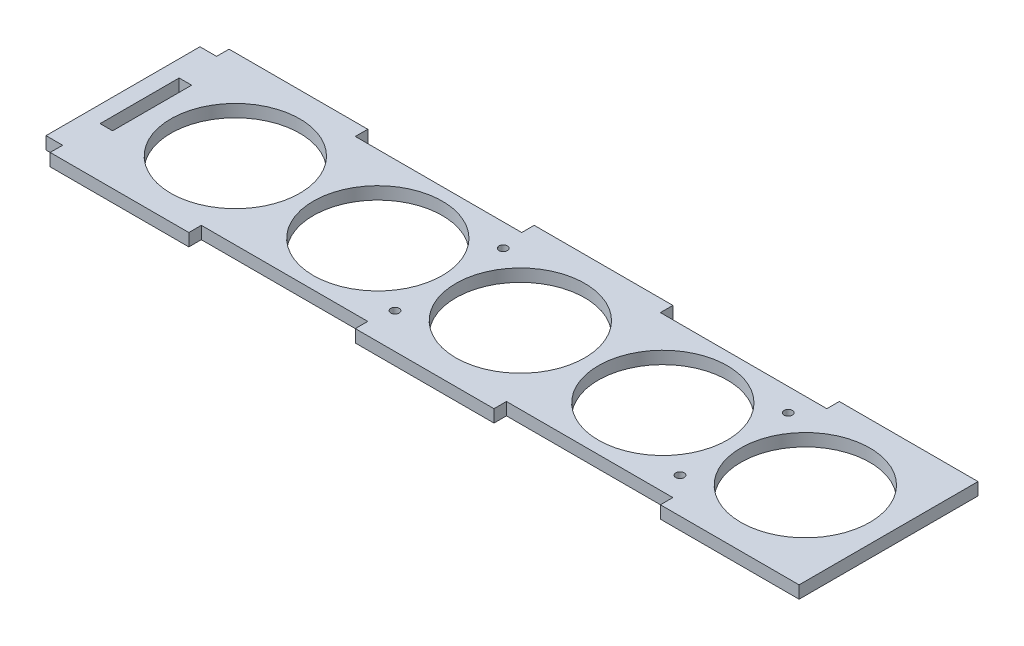
SolidWorks part; units mm, degrees
ref_plane "Front Plane" through (0, 0, 0) normal (0, 0, 1) x (1, 0, 0)
ref_plane "Top Plane" through (0, 0, 0) normal (0, 1, 0) x (1, 0, 0)
ref_plane "Right Plane" through (0, 0, 0) normal (1, 0, 0) x (0, 0, -1)
sketch "Sketch1" plane through (0, 0, 0) normal (0, 1, 0) x (1, 0, 0)
  line L0 (73.3333, 18.5) -> (106.6667, 18.5) construction
  line L1 (0, 21.5) -> (180, 21.5)
  line L2 (0, 21.5) -> (0, -21.5)
  line L3 (0, -21.5) -> (180, -21.5)
  line L4 (180, 21.5) -> (180, -21.5)
  line L5 (0, -9.5) -> (3, -9.5)
  line L6 (0, -9.5) -> (0, 9.5)
  line L7 (0, 9.5) -> (3, 9.5)
  line L8 (3, -9.5) -> (3, 9.5)
  line L9 (33.3333, 21.5) -> (73.3333, 21.5)
  line L10 (33.3333, 21.5) -> (33.3333, 18.5)
  line L11 (33.3333, 18.5) -> (73.3333, 18.5)
  line L12 (73.3333, 21.5) -> (73.3333, 18.5)
  line L13 (106.6667, 21.5) -> (146.6667, 21.5)
  line L14 (106.6667, 21.5) -> (106.6667, 18.5)
  line L15 (106.6667, 18.5) -> (146.6667, 18.5)
  line L16 (146.6667, 21.5) -> (146.6667, 18.5)
  line L17 (146.6667, 18.5) -> (180, 18.5) construction
  line L18 (33.3333, 18.5) -> (0, 18.5) construction
  line L19 (74.375, 0) -> (74.375, 13) construction
  line L20 (106.6667, -18.5) -> (146.6667, -18.5)
  line L21 (146.6667, -21.5) -> (146.6667, -18.5)
  line L22 (106.6667, -21.5) -> (146.6667, -21.5)
  line L23 (106.6667, -21.5) -> (106.6667, -18.5)
  line L24 (33.3333, -18.5) -> (73.3333, -18.5)
  line L25 (73.3333, -21.5) -> (73.3333, -18.5)
  line L26 (33.3333, -21.5) -> (73.3333, -21.5)
  line L27 (33.3333, -21.5) -> (33.3333, -18.5)
  line L28 (23, 0) -> (57.25, 0) construction
  line L29 (57.25, 0) -> (91.5, 0) construction
  line L30 (91.5, 0) -> (125.75, 0) construction
  line L31 (125.75, 0) -> (160, 0) construction
  line L32 (0, 18.5) -> (-4, 18.5)
  line L33 (0, 18.5) -> (0, -18.5)
  line L34 (0, -18.5) -> (-4, -18.5)
  line L35 (-4, 18.5) -> (-4, -18.5)
  line L36 (142.875, 0) -> (142.875, 13) construction
  circle A0 centre (23, 0) radius 15.5
  circle A1 centre (57.25, 0) radius 15.5
  circle A2 centre (91.5, 0) radius 15.5
  circle A3 centre (125.75, 0) radius 15.5
  circle A4 centre (160, 0) radius 15.5
  circle A5 centre (74.375, 13) radius 1
  circle A6 centre (142.875, 13) radius 1
  circle A7 centre (142.875, -13) radius 1
  circle A8 centre (74.375, -13) radius 1
  point P4 (0, 0)
  point P11 (3, 0)
  dimension "D6" = 23
  dimension "D7" = 31
  dimension "D10" = 13
  dimension "D11" = 2
  dimension "D12" = 2
  dimension "D1" = 43
  dimension "D2" = 180
  dimension "D3" = 19
  dimension "D4" = 3
  dimension "D5" = 40
  dimension "D8" = 20
  dimension "D9" = 4
  dimension "D13" = 13
extrude "Boss-Extrude1" add sketch "Sketch1" along normal blind 3 contours L3 L27 L24 L25 L23 L20 L21 L4 L1 L16 L15 L14 L12 L11 L10 L2 L7 L8 L5 A4 A3 A2 A1 A0 | L33 L32 L35 L34
